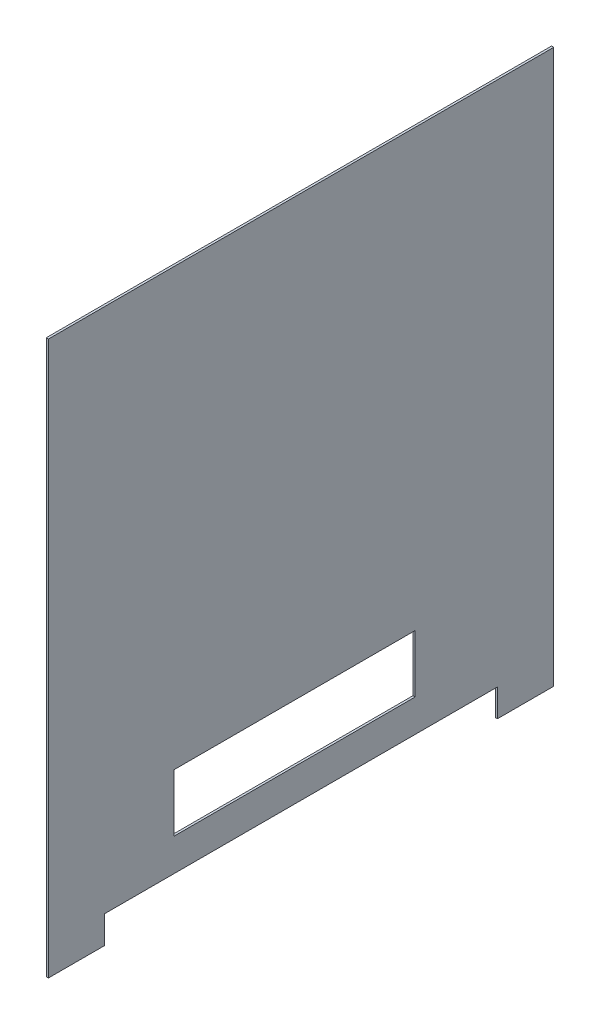
SolidWorks part; units mm, degrees
ref_plane "Front Plane" through (0, 0, 0) normal (0, 0, 1) x (1, 0, 0)
ref_plane "Top Plane" through (0, 0, 0) normal (0, 1, 0) x (1, 0, 0)
ref_plane "Right Plane" through (0, 0, 0) normal (1, 0, 0) x (0, 0, -1)
sketch "Sketch1" plane through (0, 0, 0) normal (1, 0, 0) x (0, 0, -1)
  line L1 (-173.1933, 215.5294) -> (284.8067, 215.5294)
  line L2 (-173.1933, 215.5294) -> (-173.1933, -261.0706)
  line L3 (-173.1933, -261.0706) -> (284.8067, -261.0706)
  line L4 (284.8067, 215.5294) -> (284.8067, -261.0706)
  dimension "D1" = 476.6
  dimension "D2" = 458
extrude "Boss-Extrude1" add sketch "Sketch1" along normal blind 2
sketch "Sketch2" plane through (2, 0, 0) normal (1, 0, 0) x (0, 0, -1)
  line L0 (55.8067, -261.0706) -> (55.8067, -216.267) construction
  line L1 (-173.1933, -261.0706) -> (-122.1933, -261.0706)
  line L2 (-173.1933, -261.0706) -> (-173.1933, -286.0706)
  line L3 (-173.1933, -286.0706) -> (-122.1933, -286.0706)
  line L4 (-122.1933, -261.0706) -> (-122.1933, -286.0706)
  line L5 (-173.1933, -261.0706) -> (284.8067, -261.0706) construction
  line L6 (284.8067, -286.0706) -> (233.8067, -286.0706)
  line L7 (233.8067, -261.0706) -> (233.8067, -286.0706)
  line L8 (284.8067, -261.0706) -> (233.8067, -261.0706)
  line L9 (284.8067, -261.0706) -> (284.8067, -286.0706)
  dimension "D1" = 51
  dimension "D2" = 25
extrude "Boss-Extrude2" add sketch "Sketch2" against normal blind 2
sketch "Sketch3" plane through (0, 0, 0) normal (-1, 0, 0) x (0, 0, 1)
  line L1 (-159.1435, -179.4884) -> (59.5502, -179.4884)
  line L2 (-159.1435, -179.4884) -> (-159.1435, -231.6539)
  line L3 (-159.1435, -231.6539) -> (59.5502, -231.6539)
  line L4 (59.5502, -179.4884) -> (59.5502, -231.6539)
extrude "Cut-Extrude1" cut sketch "Sketch3" against normal blind 10
